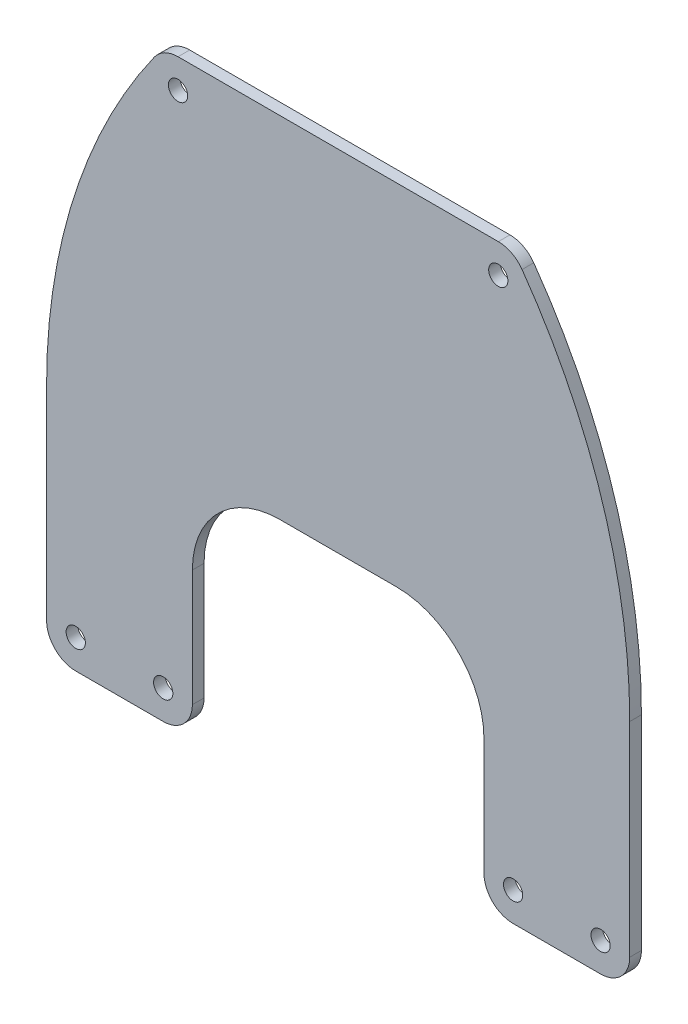
SolidWorks part; units mm, degrees
ref_plane "前视基准面" through (0, 0, 0) normal (0, 0, 1) x (1, 0, 0)
ref_plane "上视基准面" through (0, 0, 0) normal (0, 1, 0) x (1, 0, 0)
ref_plane "右视基准面" through (0, 0, 0) normal (1, 0, 0) x (0, 0, -1)
sketch "草图1" plane through (0, 0, 0) normal (0, 0, 1) x (1, 0, 0)
  line L1 (0, 0) -> (-100, 0)
  line L2 (0, 0) -> (0, 100)
  line L3 (0, 100) -> (-100, 100)
  line L4 (-100, 0) -> (-100, 100)
  line L5 (-100, 100) -> (0, 100)
  line L6 (-100, 100) -> (-100, 40)
  line L7 (-100, 40) -> (0, 40)
  line L8 (0, 100) -> (0, 40)
  line L9 (-100, 40) -> (-75, 40)
  line L10 (-100, 40) -> (-100, 0)
  line L11 (-100, 0) -> (-75, 0)
  line L12 (-75, 40) -> (-75, 0)
  line L13 (-25, 40) -> (0, 40)
  line L14 (-25, 40) -> (-25, 0)
  line L15 (-25, 0) -> (0, 0)
  line L16 (0, 40) -> (0, 0)
  arc A0 (-100, 40) -> (-80, 100) centre (0, 40) cw
  arc A1 (0, 40) -> (-20, 100) centre (-100, 40) ccw
  dimension "D1" = 100
  dimension "D2" = 100
  dimension "D3" = 60
  dimension "D4" = 25
  dimension "D5" = 25
extrude "凸台-拉伸1" add sketch "草图1" along normal blind 2 contours L7 A1 L5 A0 | L12 L7 L4 L1 | L7 L14 L1 L2
fillet "圆角1" radius 15 2 edges at (-25, 40, 1) (-75, 40, 1)
fillet "圆角2" radius 5 4 edges at (0, 0, 1) (-100, 0, 1) (-75, 0, 1) (-25, 0, 1)
fillet "圆角3" radius 5 2 edges at (-20, 100, 1) (-80, 100, 1)
sketch "草图2" plane through (0, 0, 2) normal (0, 0, 1) x (1, 0, 0)
  line L8 (-22.5403, 100) -> (-77.4597, 100)
  line L9 (-100, 40) -> (-100, 5)
  line L10 (-95, 0) -> (-80, 0)
  line L11 (-75, 5) -> (-75, 25)
  line L12 (-60, 40) -> (-40, 40)
  line L13 (-25, 25) -> (-25, 5)
  line L14 (-20, 0) -> (-5, 0)
  line L15 (0, 5) -> (0, 40)
  line L16 (-22.5403, 100) -> (-77.4597, 100)
  line L17 (-100, 40) -> (-100, 5)
  line L18 (-95, 0) -> (-80, 0)
  line L19 (-75, 5) -> (-75, 25)
  line L20 (-60, 40) -> (-40, 40)
  line L21 (-25, 25) -> (-25, 5)
  line L22 (-20, 0) -> (-5, 0)
  line L23 (0, 5) -> (0, 40)
  circle A0 centre (-77.4597, 95) radius 1.65
  circle A1 centre (-22.5403, 95) radius 1.65
  circle A2 centre (-95, 5) radius 1.65
  circle A3 centre (-5, 5) radius 1.65
  circle A4 centre (-80, 5) radius 1.65
  circle A5 centre (-20, 5) radius 1.65
  arc A10 (0, 40) -> (-18.4635, 97.8947) centre (-100, 40) ccw
  arc A11 (-18.4635, 97.8947) -> (-22.5403, 100) centre (-22.5403, 95) ccw
  arc A12 (-77.4597, 100) -> (-81.5365, 97.8947) centre (-77.4597, 95) ccw
  arc A13 (-81.5365, 97.8947) -> (-100, 40) centre (0, 40) ccw
  arc A14 (-100, 5) -> (-95, 0) centre (-95, 5) ccw
  arc A15 (-80, 0) -> (-75, 5) centre (-80, 5) ccw
  arc A16 (-60, 40) -> (-75, 25) centre (-60, 25) ccw
  arc A17 (-25, 25) -> (-40, 40) centre (-40, 25) ccw
  arc A18 (-25, 5) -> (-20, 0) centre (-20, 5) ccw
  arc A19 (-5, 0) -> (0, 5) centre (-5, 5) ccw
  arc A20 (0, 40) -> (-18.4635, 97.8947) centre (-100, 40) ccw
  arc A21 (-18.4635, 97.8947) -> (-22.5403, 100) centre (-22.5403, 95) ccw
  arc A22 (-77.4597, 100) -> (-81.5365, 97.8947) centre (-77.4597, 95) ccw
  arc A23 (-81.5365, 97.8947) -> (-100, 40) centre (0, 40) ccw
  arc A24 (-100, 5) -> (-95, 0) centre (-95, 5) ccw
  arc A25 (-80, 0) -> (-75, 5) centre (-80, 5) ccw
  arc A26 (-60, 40) -> (-75, 25) centre (-60, 25) ccw
  arc A27 (-25, 25) -> (-40, 40) centre (-40, 25) ccw
  arc A28 (-25, 5) -> (-20, 0) centre (-20, 5) ccw
  arc A29 (-5, 0) -> (0, 5) centre (-5, 5) ccw
  dimension "D2" = 3.3
  dimension "D3" = 3.3
  dimension "D4" = 3.3
  dimension "D5" = 3.3
  dimension "D6" = 3.3
  dimension "D7" = 3.3
  dimension "D1" = 0
extrude "切除-拉伸2" cut sketch "草图2" against normal blind 2 contours A0 | A1 | A2 | A4 | A5 | A3
